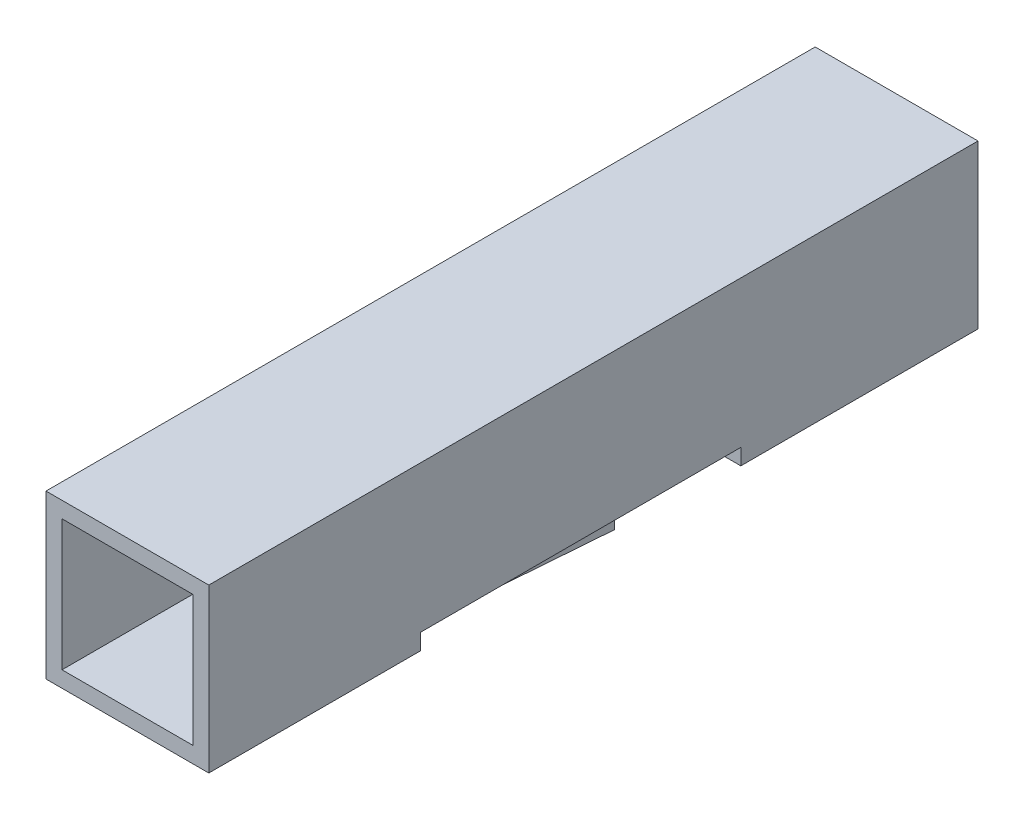
SolidWorks part; units mm, degrees
ref_plane "Front Plane" through (0, 0, 0) normal (0, 0, 1) x (1, 0, 0)
ref_plane "Top Plane" through (0, 0, 0) normal (0, 1, 0) x (1, 0, 0)
ref_plane "Right Plane" through (0, 0, 0) normal (1, 0, 0) x (0, 0, -1)
sketch "Sketch1" plane through (0, 0, 0) normal (0, 0, 1) x (1, 0, 0)
  line L0 (0.57, 0.57) -> (-0.57, 0.57)
  line L1 (1.27, 1.27) -> (-1.27, 1.27)
  line L2 (1.27, 1.27) -> (1.27, -1.27)
  line L3 (1.27, -1.27) -> (-1.27, -1.27)
  line L4 (-1.27, 1.27) -> (-1.27, -1.27)
  line L5 (1.27, 1.27) -> (-1.27, -1.27) construction
  line L6 (1.27, -1.27) -> (-1.27, 1.27) construction
  line L7 (-0.57, 0.57) -> (-0.57, -0.57)
  line L8 (0.57, -0.57) -> (-0.57, -0.57)
  line L9 (0.57, 0.57) -> (0.57, -0.57)
  point P0 (0, 0)
  dimension "D1" = 2.54
  dimension "D2" = 2.54
  dimension "D3" = 0.7
extrude "Boss-Extrude1" add sketch "Sketch1" along normal blind 12 contours L1 L4 L3 L2 L0 L9 L8 L7
sketch "Sketch2" plane through (0, 0, 12) normal (0, 0, 1) x (1, 0, 0)
  line L2 (1.27, 1.27) -> (-1.27, 1.27) construction
  line L3 (1.02, 1.02) -> (-1.02, 1.02)
  line L4 (1.02, 1.02) -> (1.02, -1.02)
  line L5 (1.02, -1.02) -> (-1.02, -1.02)
  line L6 (-1.02, 1.02) -> (-1.02, -1.02)
  line L7 (1.02, 1.02) -> (-1.02, -1.02) construction
  line L8 (1.02, -1.02) -> (-1.02, 1.02) construction
  line L9 (-1.27, 1.27) -> (-1.27, -1.27) construction
  point P2 (0, 0)
  dimension "D1" = 0.25
  dimension "D2" = 0.25
extrude "Cut-Extrude1" cut sketch "Sketch2" against normal blind 11.5
chamfer "Chamfer1" distance 0.3 angle 45 4 edges at (-0.57, 0, 0) (0, -0.57, 0) (0.57, 0, 0) (0, 0.57, 0)
sketch "Sketch3" plane through (0, -1.27, 0) normal (0, -1, 0) x (1, 0, 0)
  line L0 (-1.27, 12) -> (-1.27, 0) construction
  line L1 (-1.27, 8.7) -> (1.27, 8.7)
  line L2 (-1.27, 8.7) -> (-1.27, 3.7)
  line L3 (-1.27, 3.7) -> (1.27, 3.7)
  line L4 (1.27, 8.7) -> (1.27, 3.7)
  line L5 (1.27, 12) -> (1.27, 0) construction
  line L6 (1.27, 0) -> (-1.27, 0) construction
  dimension "D1" = 3.7
  dimension "D2" = 5
extrude "Cut-Extrude2" cut sketch "Sketch3" along direction (0, -1, 0) on the side against the normal up to surface (0.25 mm away)
sketch "Sketch4" plane through (0, 0, 0) normal (1, 0, 0) x (0, 0, -1)
  line L1 (-5.3, -1.5169) -> (-5.3, -0.7986)
  line L4 (-8.7, -1.27) -> (-5.3, -1.5169)
  line L5 (-8.7, -1.02) -> (-8.7, -1.27)
  line L6 (-5.3, -0.7986) -> (-8.7, -1.02)
extrude "Boss-Extrude2" add sketch "Sketch4" along normal mid plane 1.8
